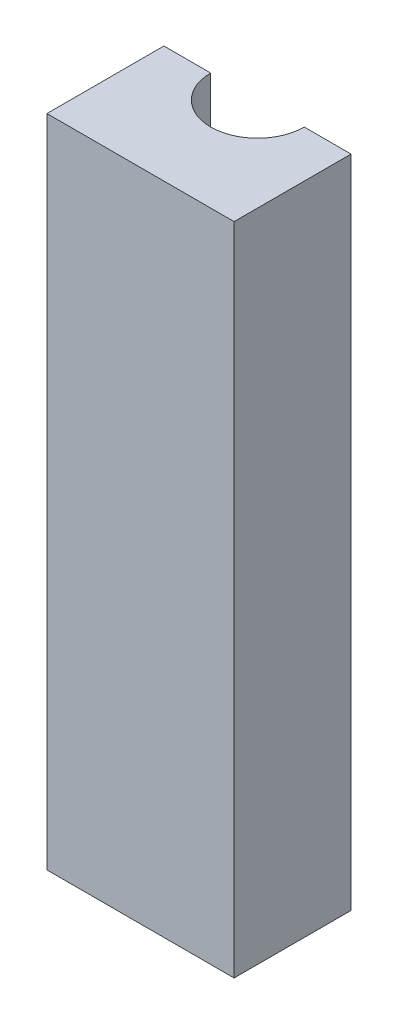
SolidWorks part; units mm, degrees
ref_plane "Front Plane" through (0, 0, 0) normal (0, 0, 1) x (1, 0, 0)
ref_plane "Top Plane" through (0, 0, 0) normal (0, 1, 0) x (1, 0, 0)
ref_plane "Right Plane" through (0, 0, 0) normal (1, 0, 0) x (0, 0, -1)
sketch "Sketch4" plane through (0, 0, 0) normal (0, 1, 0) x (1, 0, 0)
  line L0 (0, 0) -> (-20, 0)
  line L1 (-20, 0) -> (-20, -25)
  line L2 (-20, -25) -> (20, -25)
  line L3 (20, -25) -> (20, 0)
  line L4 (20, 0) -> (0, 0)
  circle A0 centre (0, 0) radius 10
  dimension "D1" = 20
  dimension "D2" = 40
  dimension "D3" = 20
  dimension "D4" = 25
extrude "Boss-Extrude1" add sketch "Sketch4" against normal blind 140 contours A0 L0 L1 L2 L3 L4
